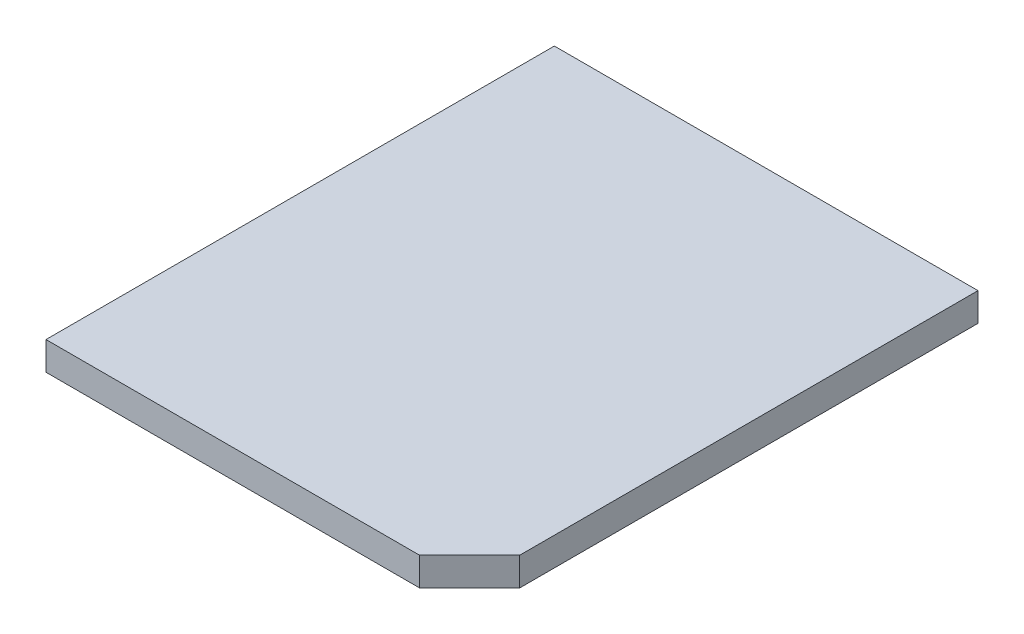
SolidWorks part; units mm, degrees
ref_plane "Front Plane" through (0, 0, 0) normal (0, 0, 1) x (1, 0, 0)
ref_plane "Top Plane" through (0, 0, 0) normal (0, 1, 0) x (1, 0, 0)
ref_plane "Right Plane" through (0, 0, 0) normal (1, 0, 0) x (0, 0, -1)
sketch "Sketch1" plane through (0, 0, 0) normal (0, 1, 0) x (1, 0, 0)
  line L1 (0, 0) -> (25.4, 0)
  line L2 (0, 0) -> (0, 30.48)
  line L3 (0, 30.48) -> (25.4, 30.48)
  line L4 (25.4, 0) -> (25.4, 30.48)
  dimension "D1" = 25.4
  dimension "D2" = 30.48
extrude "Boss-Extrude1" add sketch "Sketch1" along normal blind 1.7
chamfer "Chamfer1" distance 3 angle 45 1 edges at (25.4, 0.85, 0)
